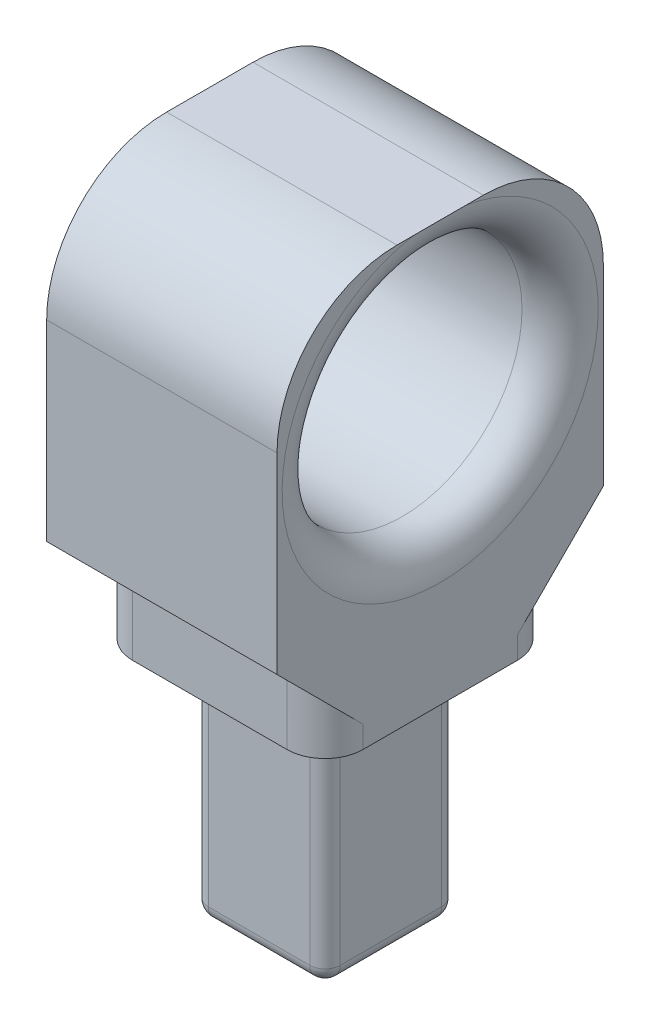
SolidWorks part; units mm, degrees
ref_plane "Front Plane" through (0, 0, 0) normal (0, 0, 1) x (1, 0, 0)
ref_plane "Top Plane" through (0, 0, 0) normal (0, 1, 0) x (1, 0, 0)
ref_plane "Right Plane" through (0, 0, 0) normal (1, 0, 0) x (0, 0, -1)
ref_plane "Plane1" through (-15.2, 0, 0) normal (-1, 0, 0) x (0, -1, 0)
sketch "Sketch1" plane through (-15.2, 0, 0) normal (-1, 0, 0) x (0, -1, 0)
  line L0 (-55, -19.2) -> (-20, -19.2)
  line L1 (-20, -19.2) -> (-20, 8)
  line L2 (-20, 8) -> (-55, 8)
  line L3 (-55, 8) -> (-55, -19.2)
extrude "Boss-Extrude1" add sketch "Sketch1" against normal blind 19.2
sketch "Sketch2" plane through (4, 0, 0) normal (1, 0, 0) x (0, 0, -1)
  line L0 (-4, 25) -> (-8, 25)
  line L1 (-8, 25) -> (-8, 20)
  line L2 (-8, 20) -> (-4, 20)
  line L3 (-4, 20) -> (-4, 25)
extrude "Cut-Extrude1" cut sketch "Sketch2" against normal through all
sketch "Sketch3" plane through (4, 0, 0) normal (1, 0, 0) x (0, 0, -1)
  line L0 (19.2, 25) -> (15.2, 25)
  line L1 (15.2, 25) -> (15.2, 20)
  line L2 (15.2, 20) -> (19.2, 20)
  line L3 (19.2, 20) -> (19.2, 25)
extrude "Cut-Extrude2" cut sketch "Sketch3" against normal through all
sketch "Sketch4" plane through (0, 20, 0) normal (0, -1, 0) x (1, 0, 0)
  line L0 (-0.1, -11.1) -> (-11.1, -11.1)
  line L1 (-11.1, -11.1) -> (-11.1, -0.1)
  line L2 (-11.1, -0.1) -> (-0.1, -0.1)
  line L3 (-0.1, -0.1) -> (-0.1, -11.1)
extrude "Boss-Extrude2" add sketch "Sketch4" along normal blind 20
draft "Draft1" type of draft neutral plane draft angle 45 faces to draft 1 face at (-5.6, 25, 6) neutral plane through (-15.2, 20, 4) neutral plane normal (0, 0, 1) parameters "D1"=45
draft "Draft2" type of draft neutral plane draft angle 45 faces to draft 1 face at (-5.6, 25, -17.2) neutral plane through (-15.2, 25, -15.2) neutral plane normal (0, 0, -1) parameters "D1"=45
ref_plane "Plane2" through (0, 0, -5.6) normal (0, 0, 1) x (1, 0, 0)
sketch "Sketch5" plane through (0, 0, -5.6) normal (0, 0, 1) x (1, 0, 0)
  line L0 (-15.2, 55.175) -> (-15.2, 42)
  line L1 (-15.2, 42) -> (4, 42)
  line L2 (4, 42) -> (4, 55.175)
  line L3 (0.825, 52) -> (-12.025, 52)
  line L4 (-15.2, 42) -> (4, 42) construction
  arc A0 (4, 55.175) -> (0.825, 52) centre (0.825, 55.175) cw
  arc A1 (-12.025, 52) -> (-15.2, 55.175) centre (-12.025, 55.175) cw
revolve "Cut-Revolve1" cut sketch "Sketch5" angle 360 about L4
fillet "Fillet1" radius 1.27 8 edges at (-0.1, 10, -11.1) (-0.1, 0, -5.6) (-0.1, 10, -0.1) (-5.6, 0, -11.1) (-11.1, 10, -11.1) (-5.6, 0, -0.1) (-11.1, 0, -5.6) (-11.1, 10, -0.1)
fillet "Fillet2" radius 3.175 4 edges at (-15.2, 22.5, 4) (4, 22.5, 4) (-15.2, 22.5, -15.2) (4, 22.5, -15.2)
fillet "Fillet3" radius 10 2 edges at (-5.6, 55, -19.2) (-5.6, 55, 8)
